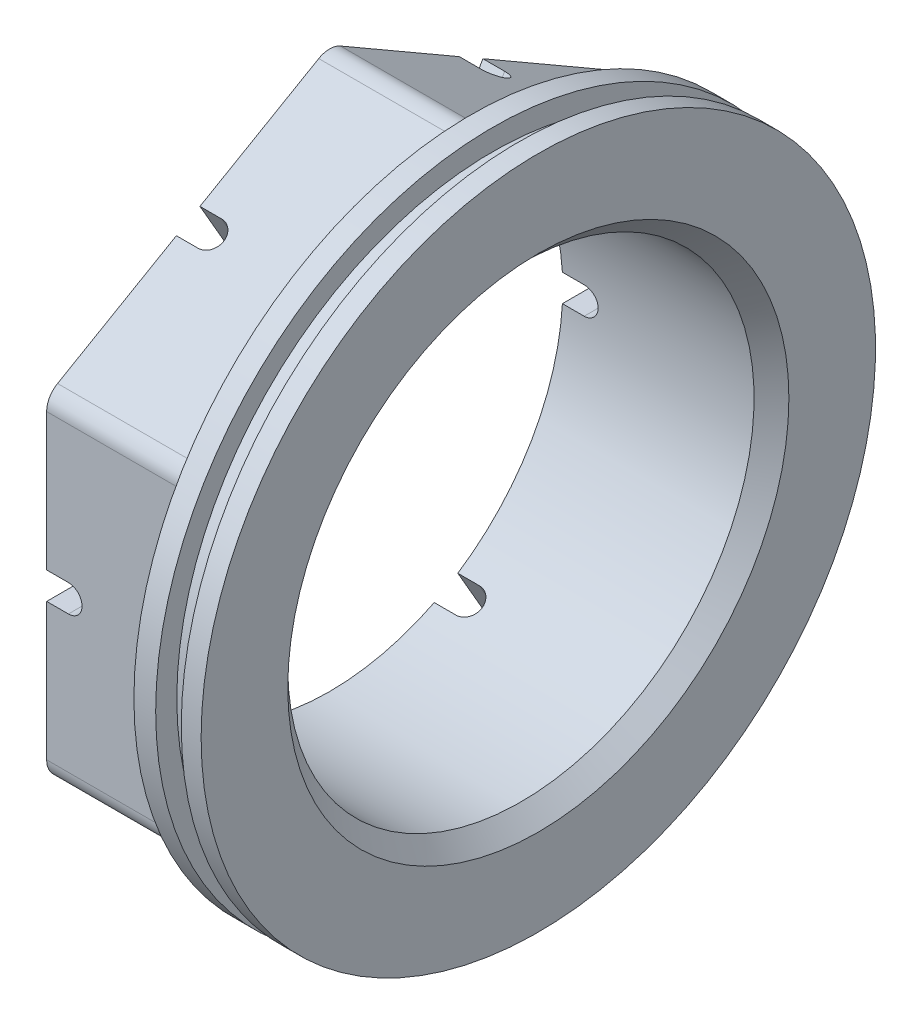
SolidWorks part; units mm, degrees
material "6061-T6 (SS)"
ref_plane "X-Y Datum" through (0, 0, 0) normal (0, 0, 1) x (1, 0, 0)
ref_plane "X-Z Datum" through (0, 0, 0) normal (0, 1, 0) x (1, 0, 0)
ref_plane "Y-Z Datum" through (0, 0, 0) normal (1, 0, 0) x (0, 0, -1)
sketch "Sketch2" plane through (0, 0, 0) normal (0, 0, 1) x (1, 0, 0)
  line L0 (0, 0) -> (0, 29100.2887) construction
  line L1 (0, 0) -> (29100.2887, 0) construction
  line L10 (-25.6794, 49.1871) -> (-6.6294, 49.1871)
  line L12 (-6.6294, 49.1871) -> (-1.8669, 49.1871)
  line L13 (-1.8669, 49.1871) -> (-1.8669, 46.1056)
  line L14 (-1.8669, 46.1056) -> (1.8669, 46.1056)
  line L15 (1.8669, 46.1056) -> (1.8669, 49.1871)
  line L16 (1.8669, 49.1871) -> (4.7625, 49.1871)
  line L17 (4.7625, 49.1871) -> (4.7625, 34.0106)
  line L18 (4.7625, 34.0106) -> (-25.6794, 34.0106)
  line L19 (-25.6794, 34.0106) -> (-25.6794, 49.1871)
  line L20 (4.7625, 49.2125) -> (-22.4282, 49.2125) construction
  point P17 (0, 46.1056)
  dimension "D2" = 68.0212
  dimension "D4" = 98.3742
  dimension "D5" = 3.7338
  dimension "D6" = 19.05
  dimension "D7" = 4.7625
  dimension "D3" = 4.7625
  dimension "D8" = 98.425
  dimension "D1" = 92.2111
revolve "Revolve1" add sketch "Sketch2" angle 360 about L1
sketch "Sketch3" plane through (-25.6794, 0, 0) normal (-1, 0, 0) x (0, 0, 1)
  line L0 (0, 0) -> (0, 50000) construction
  line L1 (41.275, 23.8301) -> (0, 47.6603)
  line L2 (0, 47.6603) -> (-41.275, 23.8301)
  line L3 (-41.275, 23.8301) -> (-41.275, -23.8301)
  line L4 (-41.275, -23.8301) -> (0, -47.6603)
  line L5 (0, -47.6603) -> (41.275, -23.8301)
  line L6 (41.275, -23.8301) -> (41.275, 23.8301)
  line L7 (0, 0) -> (50000, 0) construction
  circle A0 centre (0, 0) radius 41.275 construction
  circle A1 centre (0, 0) radius 49.1871 construction
  circle A2 centre (0, 0) radius 49.1871 construction
  circle M3 centre (0, 0) radius 49.1871
  dimension "D1" = 82.55
extrude "Cut-Extrude1" cut sketch "Sketch3" against normal offset from surface (20.6375 mm away) 3.175 contours L4 M3 | L3 M3 | L5 M3 | L6 M3 | L1 M3 | L2 M3
fillet "Fillet3" radius 3.175 6 edges at (-15.3606, 47.6603, 0) (-15.3606, 23.8301, 41.275) (-15.3606, -23.8301, 41.275) (-15.3606, -47.6603, 0) (-15.3606, -23.8301, -41.275) (-15.3606, 23.8301, -41.275)
chamfer "Chamfer1" distance 2.54 angle 45 1 edges at (4.7625, 0, 34.0106)
thread "Thread3" pitch 2.1167 start angle 0, offset 6.35, length 0, pitch 2.1167, diameter 69.85
ref_plane "Plane2" through (-32.0294, 0, -34.925) normal (0, -1, 0) x (0, 0, -1)
sketch "Thread Profile2" plane through (-32.0294, 0, -34.925) normal (0, -1, 0) x (0, 0, -1)
  line L0 (0, 0) -> (0, 2.1167) construction
  line L11 (0, 0) -> (0, 1.8521)
  line L12 (0, 1.8521) -> (-1.1457, 1.1906)
  line L13 (-1.1457, 1.1906) -> (-1.1457, 0.6615)
  line L15 (-1.1457, 0.6615) -> (0, 0)
  line L17 (-1.1457, 0.926) -> (0, 0.926) construction
  point P2 (0, 0)
  dimension "Pitch" = 2.1167
  dimension "Profile_Angle" = 60
  dimension "Profile_Land" = 0.5292
  dimension "Profile_Height" = 1.1457
sketch "Sketch4" plane through (0, 0, -41.275) normal (0, 0, -1) x (-1, 0, 0)
  line L0 (25.6794, -1.9845) -> (25.6794, 1.9845)
  line L1 (25.6794, 21.997) -> (25.6794, -21.997) construction
  line L2 (25.6794, 1.9845) -> (22.5044, 1.9845)
  line L3 (25.6794, -1.9845) -> (22.5044, -1.9845)
  line L4 (25.6794, 21.997) -> (25.6794, -21.997) construction
  arc A0 (22.5044, -1.9845) -> (22.5044, 1.9845) centre (22.5044, 0) cw
  point P8 (25.6794, 0)
  dimension "D1" = 1.9845
  dimension "D2" = 3.175
extrude "Cut-Extrude2" cut sketch "Sketch4" against normal through all
pattern_circular "CirPattern1" count 6 over 360 about axis through (0, 0, 0) along (1, 0, 0) of "Cut-Extrude2"
equation "\"D1@Sketch2\"=\"D8@Sketch2\"-.12232*2"
